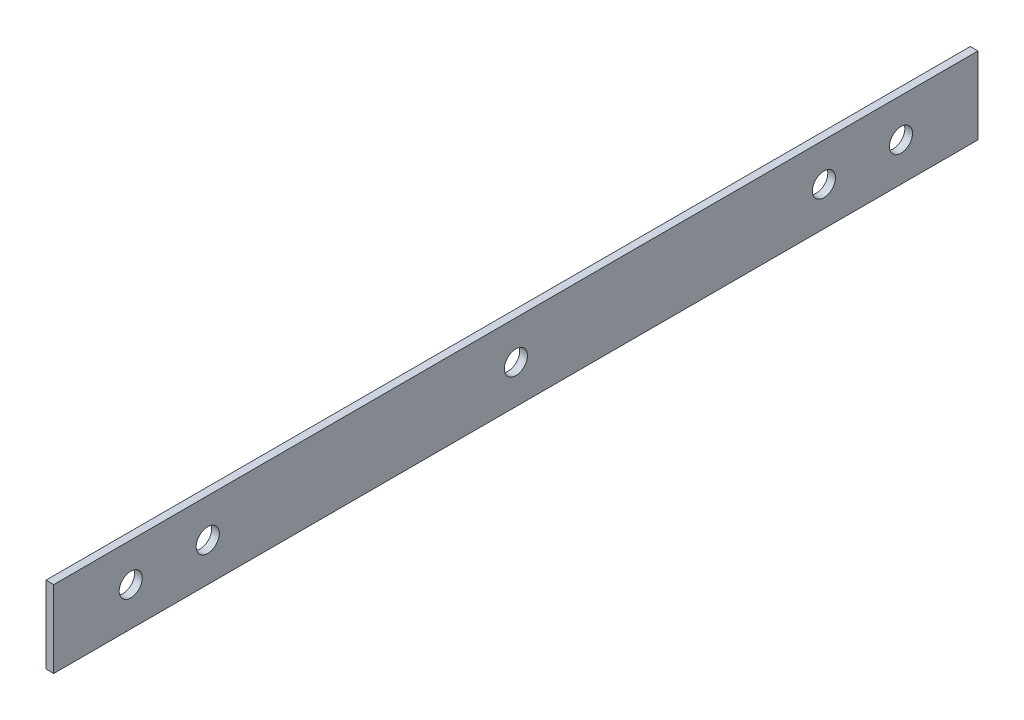
SolidWorks part; units mm, degrees
ref_plane "前视基准面" through (0, 0, 0) normal (0, 0, 1) x (1, 0, 0)
ref_plane "上视基准面" through (0, 0, 0) normal (0, 1, 0) x (1, 0, 0)
ref_plane "右视基准面" through (0, 0, 0) normal (1, 0, 0) x (0, 0, -1)
sketch "草图1" plane through (0, 0, 0) normal (1, 0, 0) x (0, 0, -1)
  line L0 (-102.9523, 3.151) -> (17.0477, 3.151)
  line L1 (-102.9523, 3.151) -> (-102.9523, -6.849)
  line L2 (-102.9523, -6.849) -> (17.0477, -6.849)
  line L3 (17.0477, 3.151) -> (17.0477, -6.849)
  line L4 (-42.9523, 8.6543) -> (-42.9523, -16.2075) construction
  circle A0 centre (-82.9523, -1.849) radius 1.5
  circle A1 centre (-2.9523, -1.849) radius 1.5
  circle A2 centre (-92.9523, -1.849) radius 1.5
  circle A3 centre (7.0477, -1.849) radius 1.5
  circle A4 centre (-42.9523, -1.849) radius 1.5
  point P18 (-102.9523, -3.3359)
  point P19 (7.4003, -3.307)
  dimension "D3" = 3
  dimension "D4" = 3
  dimension "D8" = 5
  dimension "D9" = 3
  dimension "D13" = 3
  dimension "D17" = 3
  dimension "D1" = 10
  dimension "D2" = 120
  dimension "D5" = 20
  dimension "D6" = 20
  dimension "D7" = 5
  dimension "D10" = 5
  dimension "D11" = 5
  dimension "D12" = 10
  dimension "D14" = 5
  dimension "D15" = 10
  dimension "D16" = 60
extrude "凸台-拉伸1" add sketch "草图1" along normal blind 1
